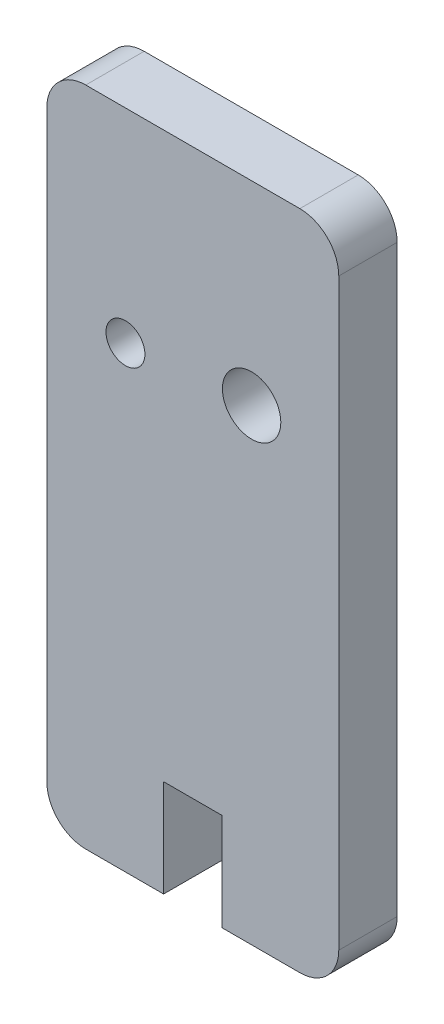
SolidWorks part; units mm, degrees
material "Acrylic (Medium-high impact)"
ref_plane "Front Plane" through (0, 0, 0) normal (0, 0, 1) x (1, 0, 0)
ref_plane "Top Plane" through (0, 0, 0) normal (0, 1, 0) x (1, 0, 0)
ref_plane "Right Plane" through (0, 0, 0) normal (1, 0, 0) x (0, 0, -1)
sketch "Sketch1" plane through (0, 0, 0) normal (0, 0, 1) x (1, 0, 0)
  line L0 (2.005, 24) -> (15, 24) construction
  line L1 (2, 0) -> (13, 0)
  line L2 (0, 2) -> (0, 32)
  line L3 (2, 34) -> (13, 34)
  line L4 (15, 2) -> (15, 32)
  line L6 (10.5217, 24) -> (0, 23.2421) construction
  circle A0 centre (10.5217, 24) radius 1.5
  circle A1 centre (4.0385, 23.533) radius 1
  arc A2 (13, 0) -> (15, 2) centre (13, 2) ccw
  arc A3 (2, 0) -> (0, 2) centre (2, 2) cw
  arc A4 (13, 34) -> (15, 32) centre (13, 32) cw
  arc A5 (0, 32) -> (2, 34) centre (2, 32) cw
  point P22 (15, 0)
  point P25 (0, 0)
  point P28 (15, 34)
  dimension "D4" = 3
  dimension "D5" = 2
  dimension "D8" = 2
  dimension "D1" = 30
  dimension "D2" = 15
  dimension "D3" = 10.467
  dimension "D6" = 6.5
  dimension "D7" = 4.12
extrude "Boss-Extrude1" add sketch "Sketch1" along normal blind 3
sketch "Sketch3" plane through (0, 0, 3) normal (0, 0, 1) x (1, 0, 0)
  line L0 (7.5, 0) -> (7.5, 34) construction
  line L1 (2, 0) -> (13, 0) construction
  line L2 (13, 34) -> (2, 34) construction
sketch "Sketch4" plane through (0, 0, 3) normal (0, 0, 1) x (1, 0, 0)
  line L0 (6, 0) -> (6, 5)
  line L1 (2, 0) -> (13, 0) construction
  line L2 (6, 5) -> (9, 5)
  line L3 (9, 5) -> (9, 0)
  line L4 (9, 0) -> (6, 0)
  line L5 (7.5, 34) -> (7.5, 5) construction
  line L6 (13, 34) -> (2, 34) construction
  dimension "D1" = 3
  dimension "D2" = 5
extrude "Cut-Extrude1" cut sketch "Sketch4" against normal through all
